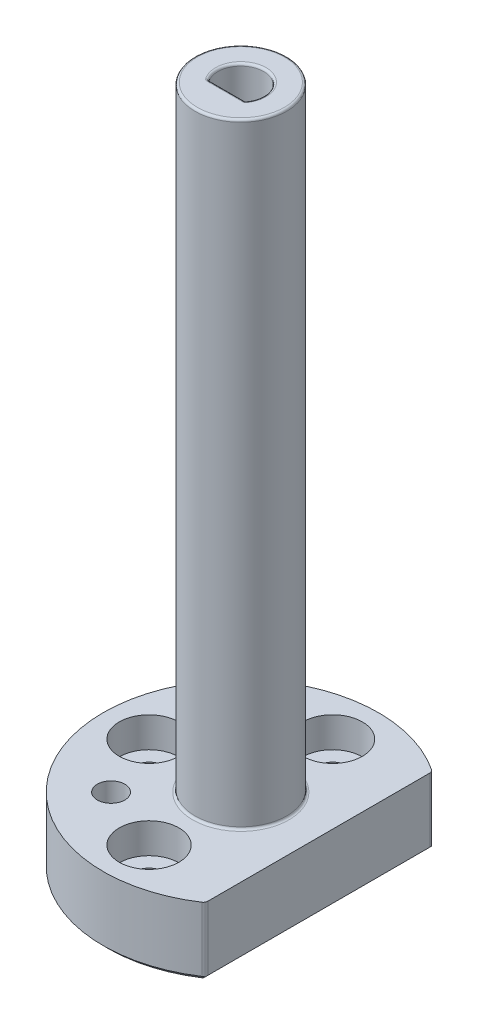
SolidWorks part; units mm, degrees
material "1.0045 (S355JR)"
ref_plane "Front Plane" through (0, 0, 0) normal (0, 0, 1) x (1, 0, 0)
ref_plane "Top Plane" through (0, 0, 0) normal (0, 1, 0) x (1, 0, 0)
ref_plane "Right Plane" through (0, 0, 0) normal (1, 0, 0) x (0, 0, -1)
sketch "Sketch1" plane through (0, 0, 0) normal (0, 1, 0) x (1, 0, 0)
  line L0 (0, 0) -> (0, 30) construction
  line L1 (17, -24.7184) -> (17, 24.7184)
  arc A0 (17, 24.7184) -> (17, -24.7184) centre (0, 0) ccw
  dimension "D1" = 60
  dimension "D2" = 17
extrude "Boss-Extrude1" add sketch "Sketch1" along normal blind 15
sketch "Sketch2" plane through (0, 15, 0) normal (0, 1, 0) x (1, 0, 0)
  circle A0 centre (0, 0) radius 10
  dimension "D1" = 20
extrude "Boss-Extrude2" add sketch "Sketch2" along normal blind 134
sketch "Sketch4" plane through (0, 0, 0) normal (0, -1, 0) x (1, 0, 0)
  circle A0 centre (0, 0) radius 7.25
  dimension "D1" = 14.5
extrude "Cut-Extrude1" cut sketch "Sketch4" against normal blind 57
sketch "Sketch5" plane through (0, 57, 0) normal (0, -1, 0) x (1, 0, 0)
  line L0 (-4, 3) -> (4, 3)
  arc A0 (-4, 3) -> (4, 3) centre (0, 0) ccw
  point P5 (0, 3)
  dimension "D1" = 10
  dimension "D2" = 3
extrude "Cut-Extrude2" cut sketch "Sketch5" against normal through all
sketch "Sketch7" plane through (0, 15, 0) normal (0, 1, 0) x (1, 0, 0)
  line L0 (0, 0) -> (-30, 0) construction
  circle A0 centre (0, -20) radius 6.5
  circle A3 centre (-20, 0) radius 6.5
  circle A6 centre (0, 20) radius 6.5 [skipped]
  circle A7 centre (20, 0) radius 6.5 [skipped]
  circle A8 centre (0, 0) radius 30 construction
  circle A9 centre (0, 20) radius 6.5
  point P9 (0, 0)
  point P13 (0, 0)
  dimension "D2" = 13
  dimension "D1" = 20
  dimension "D3" = 4
extrude "Cut-Extrude3" cut sketch "Sketch7" against normal blind 6.6
sketch "Sketch8" plane through (0, 8.4, 0) normal (0, 1, 0) x (1, 0, 0)
  line L0 (0, 0) -> (-30, 0) construction
  circle A0 centre (0, -20) radius 3.2
  circle A3 centre (-20, 0) radius 3.2
  circle A6 centre (0, 20) radius 3.2 [skipped]
  circle A7 centre (20, 0) radius 3.2 [skipped]
  circle A8 centre (0, 0) radius 30 construction
  circle A9 centre (0, 20) radius 3.2
  point P14 (0, 0)
  dimension "D1" = 6.4
  dimension "D2" = 4
  dimension "D4" = 20
extrude "Cut-Extrude4" cut sketch "Sketch8" against normal through all
fillet "Fillet1" radius 0.25 2 edges at (-4, 103, 3) (4, 103, 3)
chamfer "Chamfer1" distance 1 angle 45 2 edges at (-30, 0, 0) (17, 0, 0)
fillet "Fillet2" radius 0.5 1 edges at (0, 149, 10)
fillet "Fillet3" radius 0.5 4 edges at (-3.9877, 149, 2.9721) (3.9877, 149, 2.9721) (0, 149, 3) (0, 149, -5)
fillet "Fillet4" radius 0.5 1 edges at (0, 15, 10)
sketch "Sketch9" plane through (0, 15, 0) normal (0, 1, 0) x (1, 0, 0)
  line L0 (0, 0) -> (-30, 0) construction
  line L1 (-14.1421, -14.1421) -> (0, 0) construction
  circle A0 centre (-14.1421, -14.1421) radius 3
  arc A1 (17, 24.7184) -> (17, -24.7184) centre (0, 0) ccw construction
  dimension "D1" = 6
  dimension "D2" = 20
  dimension "D3" = 45
extrude "Cut-Extrude5" cut sketch "Sketch9" against normal through all
fillet "Fillet5" radius 1 2 edges at (17, 8, -24.7184) (17, 8, 24.7184)
